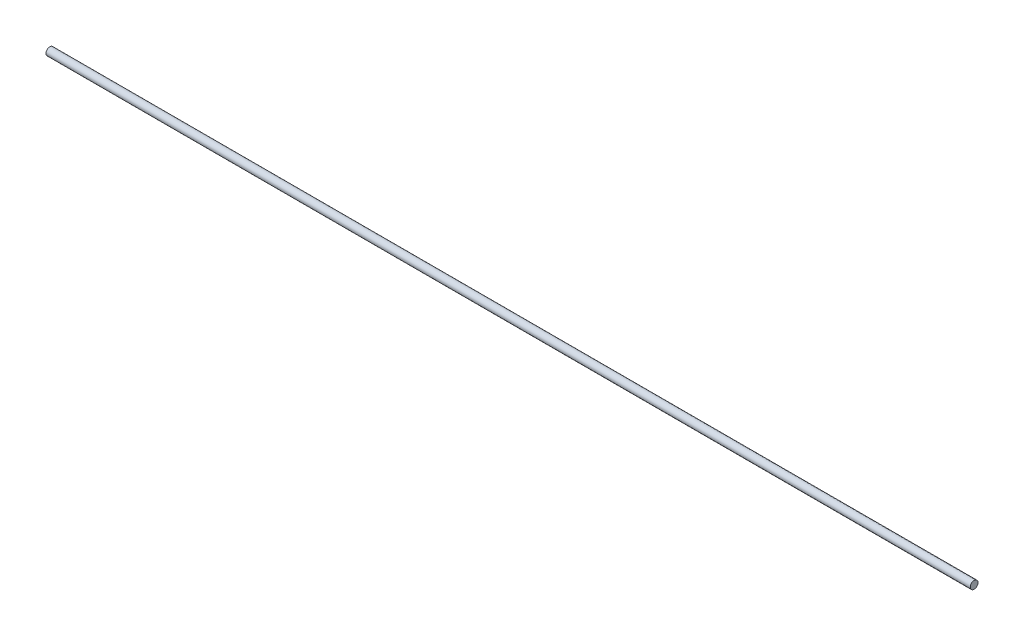
SolidWorks part; units mm, degrees
ref_plane "Front Plane" through (0, 0, 0) normal (0, 0, 1) x (1, 0, 0)
ref_plane "Top Plane" through (0, 0, 0) normal (0, 1, 0) x (1, 0, 0)
ref_plane "Right Plane" through (0, 0, 0) normal (1, 0, 0) x (0, 0, -1)
sketch "Sketch1" plane through (0, 0, 0) normal (1, 0, 0) x (0, 0, -1)
  circle A0 centre (0, 0) radius 3.175
  dimension "D1" = 6.35
extrude "Boss-Extrude1" add sketch "Sketch1" along normal blind 762
